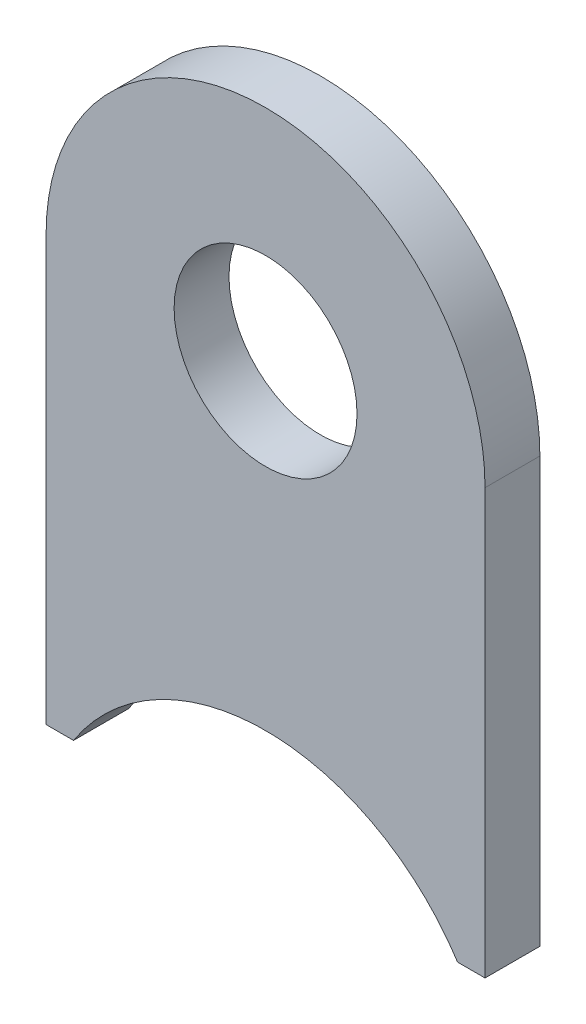
SolidWorks part; units mm, degrees
ref_plane "Płaszczyzna przednia" through (0, 0, 0) normal (0, 0, 1) x (1, 0, 0)
ref_plane "Płaszczyzna górna" through (0, 0, 0) normal (0, 1, 0) x (1, 0, 0)
ref_plane "Płaszczyzna prawa" through (0, 0, 0) normal (1, 0, 0) x (0, 0, -1)
ref_plane "Płaszczyzna1" through (0, 0, -1.5) normal (0, 0, -1) x (-1, 0, 0)
sketch "Szkic1" plane through (0, 0, -1.5) normal (0, 0, -1) x (-1, 0, 0)
  line L0 (-12, 0) -> (-12, -23.2177)
  line L1 (-12, -23.2177) -> (-10.5, -23.2177)
  line L2 (10.5, -23.2177) -> (12, -23.2177)
  line L3 (12, -23.2177) -> (12, 0)
  circle A0 centre (0, 0) radius 5
  arc A1 (-10.5, -23.2177) -> (10.5, -23.2177) centre (0, -30) cw
  arc A2 (12, 0) -> (-12, 0) centre (0, 0) ccw
  dimension "D1" = 10
  dimension "D2" = 12.5
  dimension "D3" = 12
  dimension "D4" = 1.5
  dimension "D5" = 30
extrude "Dodanie-wyciągnięcie1" add sketch "Szkic1" against normal blind 3
